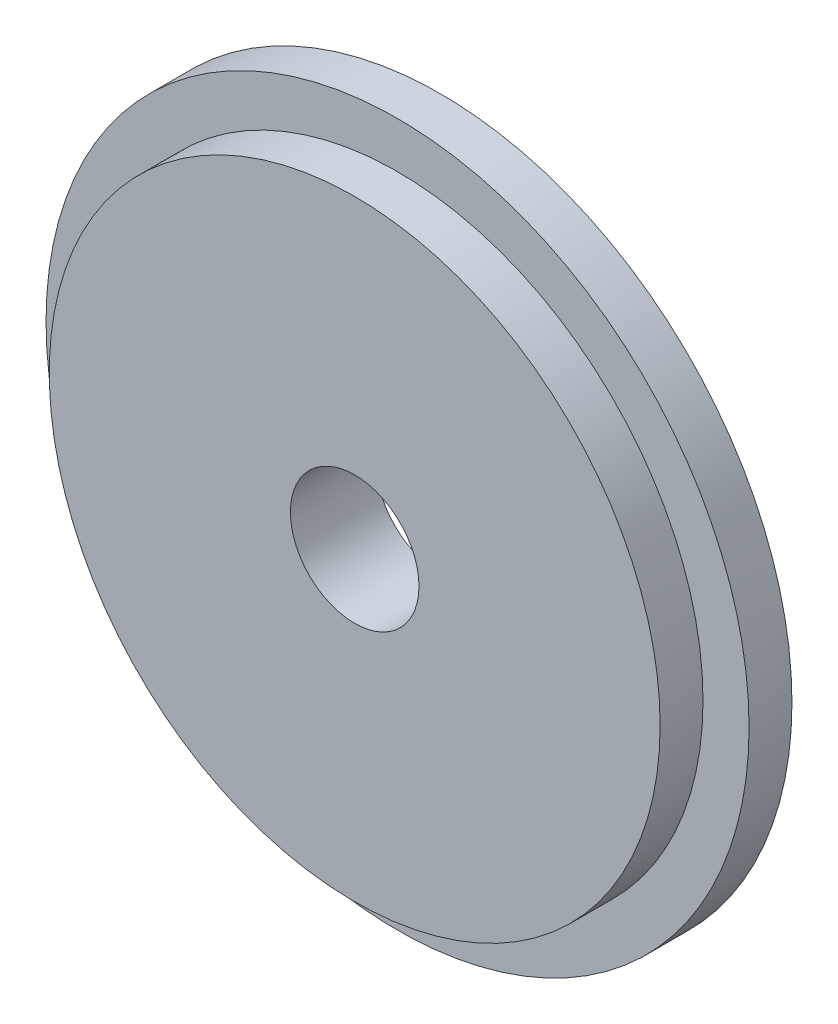
SolidWorks part; units mm, degrees
ref_plane "Plan de face" through (0, 0, 0) normal (0, 0, 1) x (1, 0, 0)
ref_plane "Plan de dessus" through (0, 0, 0) normal (0, 1, 0) x (1, 0, 0)
ref_plane "Plan de droite" through (0, 0, 0) normal (1, 0, 0) x (0, 0, -1)
sketch "Esquisse1" plane through (0, 0, 0) normal (0, 0, 1) x (1, 0, 0)
  circle A0 centre (0, 0) radius 16.4
  dimension "D1" = 32.8
extrude "Boss.-Extru.1" add sketch "Esquisse1" along normal blind 2
sketch "Esquisse2" plane through (0, 0, 2) normal (0, 0, 1) x (1, 0, 0)
  circle A0 centre (0, 0) radius 14.25
  dimension "D1" = 28.5
extrude "Boss.-Extru.2" add sketch "Esquisse2" along normal blind 2
sketch "Esquisse3" plane through (0, 0, 4) normal (0, 0, 1) x (1, 0, 0)
  circle A0 centre (0, 0) radius 3
  dimension "D1" = 6
extrude "Enlèv. mat.-Extru.1" cut sketch "Esquisse3" against normal through all
